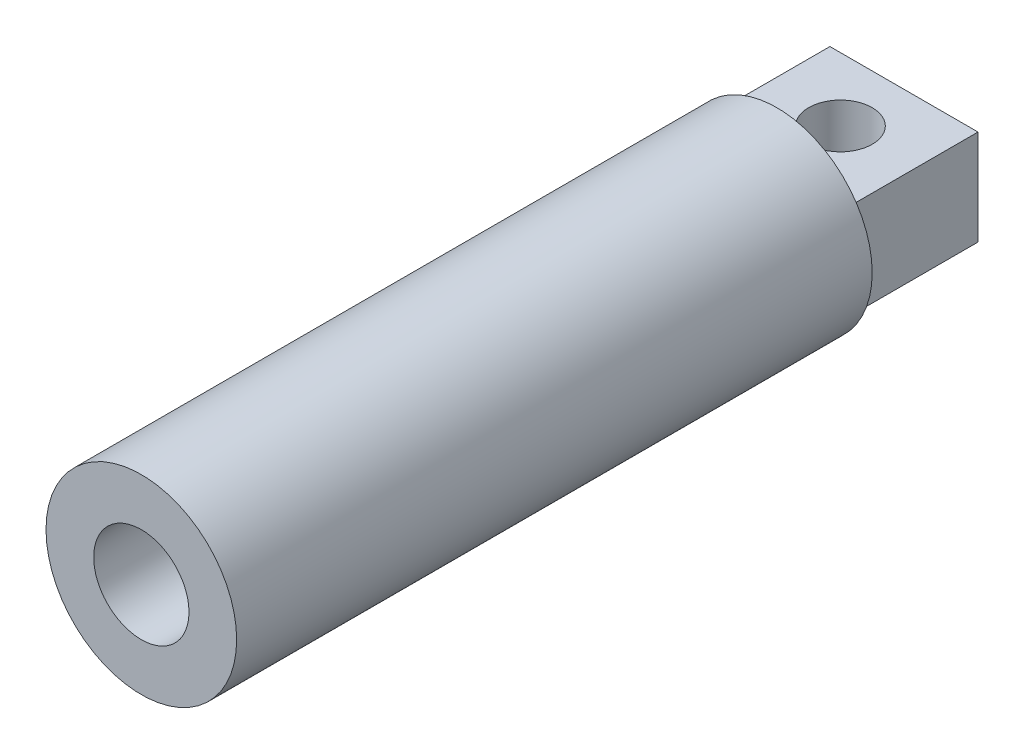
SolidWorks part; units mm, degrees
ref_plane "Front Plane" through (0, 0, 0) normal (0, 0, 1) x (1, 0, 0)
ref_plane "Top Plane" through (0, 0, 0) normal (0, 1, 0) x (1, 0, 0)
ref_plane "Right Plane" through (0, 0, 0) normal (1, 0, 0) x (0, 0, -1)
sketch "Sketch1" plane through (0, 0, 0) normal (0, 0, 1) x (1, 0, 0)
  circle A0 centre (0, 0) radius 15
  dimension "D1" = 30
extrude "Boss-Extrude1" add sketch "Sketch1" along normal blind 100
sketch "Sketch2" plane through (0, 0, 100) normal (0, 0, 1) x (1, 0, 0)
  circle A0 centre (0, 0) radius 7.5
  dimension "D1" = 15
extrude "Cut-Extrude1" cut sketch "Sketch2" against normal blind 130
sketch "Sketch3" plane through (0, 0, 0) normal (0, 1, 0) x (1, 0, 0)
  line L0 (0, 20) -> (0, 0) construction
  line L1 (-11.6503, -20) -> (11.6503, -20)
  line L2 (-11.6503, -20) -> (-11.6503, 20)
  line L3 (-11.6503, 20) -> (11.6503, 20)
  line L4 (11.6503, -20) -> (11.6503, 20)
  line L5 (-11.6503, -20) -> (11.6503, 20) construction
  line L6 (-11.6503, 20) -> (11.6503, -20) construction
  line L7 (15, 0) -> (-15, 0) construction
  circle A1 centre (0, 10) radius 5
  point P12 (0, 0)
  dimension "D3" = 10
  dimension "D4" = 10
  dimension "D1" = 20
  dimension "D2" = 40
extrude "Boss-Extrude2" add sketch "Sketch3" along normal mid plane 15
equation "\"q0\"=11.0243"
